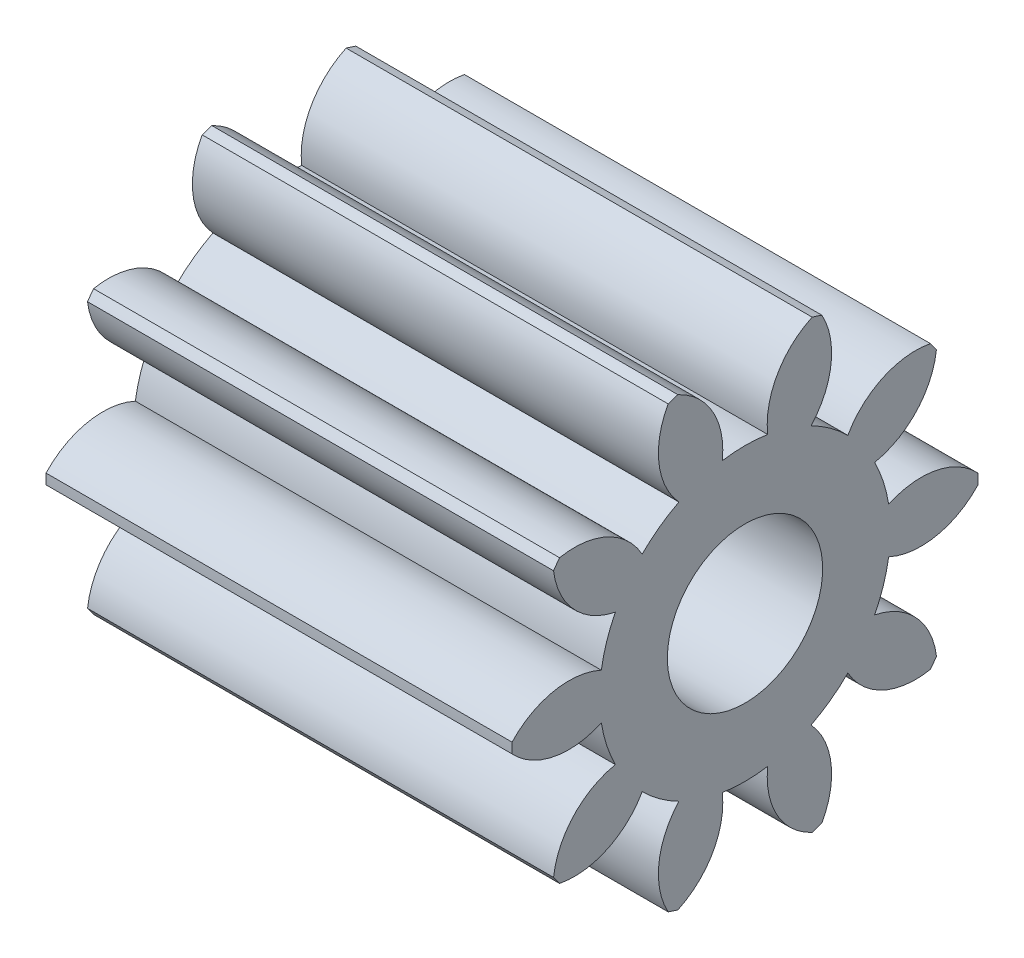
SolidWorks part; units mm, degrees
ref_plane "Plane1" through (0, 0, 0) normal (0, 0, 1) x (1, 0, 0)
ref_plane "Plane2" through (0, 0, 0) normal (0, 1, 0) x (1, 0, 0)
ref_plane "Plane3" through (0, 0, 0) normal (1, 0, 0) x (0, 0, -1)
sketch "HoldingSke" plane through (0, 0, 0) normal (0, 1, 0) x (1, 0, 0)
  line L0 (0, 0) -> (3.9392, -0.6946)
  line L1 (-15, 0) -> (100, 0) construction
  line L2 (0, 0) -> (-2.1039, 2.3779)
  line L3 (0, 0) -> (-11.863, 4.5341)
  line L4 (0, 0) -> (8.5048, 1.4996)
  line L5 (0, 0) -> (-46.8476, -17.4728)
  line L6 (0, 0) -> (-2.4869, -1.6779)
  line L7 (-2.1039, 2.3779) -> (8.6586, 51.2059)
  line L8 (-76.2, 54.61) -> (-76.1, 54.61)
  line L9 (-71.009, 38.7566) -> (-53.1078, 45.2721)
  line L10 (-76.2, 71.12) -> (104.1128, 71.12)
  line L11 (0, 0) -> (-3, 0)
  line L12 (-76.2, 101.6) -> (-76.192, 101.6)
  line L13 (24.9733, 27.94) -> (52.9518, 28.4284)
  line L14 (24.9733, 27.94) -> (24.9743, 27.94)
  line L15 (24.9733, 27.94) -> (100.4006, 29.5858)
  line L16 (-63.627, -0.25) -> (-12.827, -0.25)
  circle A0 centre (0, 0) radius 0.5
  circle A1 centre (0, 0) radius 0.9365
  circle A2 centre (0, 0) radius 37.5
  circle A3 centre (0, 0) radius 0.5
  dimension "MHD" = 1.873
  dimension "Hub_dia" = 75
  dimension "Bore" = 1
  dimension "MBD" = 1
  dimension "Num_teeth" = 10
  dimension "Pitch" = 4
  dimension "Overall_len" = 50
  dimension "Show_teeth" = 10
  dimension "Thickness" = 3
  dimension "OAL" = 50.0001
  dimension "T_dim" = 0.1
  dimension "Ap" = 20
  dimension "H" = 19.05
  dimension "Pitch_radius" = 180.3128
  dimension "Width" = 3
  dimension "Backlash" = 0.008
  dimension "Addendum_fac" = 1
  dimension "Dedendum_fac" = 1.25
  dimension "Clearance_fac" = 0.25
  dimension "Dedendum_add" = 0.001
  dimension "Module" = 0.25
sketch "BasProSke" plane through (0, 0, 0) normal (0, 1, 0) x (1, 0, 0)
  line L0 (-10, 0) -> (60, 0) construction
  line L1 (0, 0) -> (0, 1.5)
  line L2 (0, 0) -> (3, 0)
  line L3 (3, 0) -> (3, 1.5)
  line L4 (3, 1.5) -> (0, 1.5)
  dimension "Thickness" = 3
  dimension "Diameter" = 3
revolve "Base-Revolve" add sketch "BasProSke" angle 360 about L0
sketch "TooCutSke" plane through (0, 0, 0) normal (1, 0, 0) x (0, 0, -1)
  line L1 (0, 0) -> (0, 107) construction
  line L2 (0, 0) -> (-0.2095, 1.2323) construction
  line L3 (0, 0) -> (-0.7644, 2.3524) construction
  line L4 (-0.2095, 1.2323) -> (-0.3822, 1.1762) construction
  arc A0 (0.1463, 0.925) -> (-0.1463, 0.925) centre (0, 0) ccw
  arc A1 (0.4686, 1.4516) -> (-0.4686, 1.4516) centre (0, 0) ccw
  circle A2 centre (0, 0) radius 1.25 construction
  circle A3 centre (0, 0) radius 1.1746 construction
  arc A4 (-0.1463, 0.925) -> (-0.4686, 1.4516) centre (-0.6429, 0.983) ccw
  arc A5 (0.4686, 1.4516) -> (0.1463, 0.925) centre (0.6429, 0.983) ccw
  dimension "Root_dia" = 1.873
  dimension "Overcut_dia" = 3.0508
  dimension "Pitch_dia" = 2.5
  dimension "Base_dia" = 2.3492
  dimension "Flank_rad" = 0.5
  dimension "Half_ang" = 18
  dimension "Half_CT" = 0.1815
extrude "ToothCut" cut sketch "TooCutSke" along normal through all
fillet "Breaks" [suppressed] radius 0.005
fillet "RootFillets" [suppressed] radius 0.0635
pattern_circular "TeethCuts" count 10 every 36 about axis through (-10, 0, 0) along (1, 0, 0) of "ToothCut", "RootFillets", "Breaks"
sketch "HubNeaOneSke" plane through (0, 0, 0) normal (-1, 0, 0) x (0, 0, 1)
  circle A0 centre (0, 0) radius 0.9365
  dimension "Diameter" = 1.873
extrude "HubNearOne" [suppressed] add sketch "HubNeaOneSke" along normal blind 47.0001
sketch "HubNeaBotSke" plane through (0, 0, 0) normal (-1, 0, 0) x (0, 0, 1)
  circle A0 centre (0, 0) radius 0.9365
  dimension "Diameter" = 1.873
extrude "HubNearBoth" [suppressed] add sketch "HubNeaBotSke" along normal blind 23.5
ref_plane "FarPln" through (3, 0, 0) normal (1, 0, 0) x (0, 0, -1)
sketch "HubFarSke" plane through (3, 0, 0) normal (1, 0, 0) x (0, 0, -1)
  circle A0 centre (0, 0) radius 0.9365
  dimension "Diameter" = 1.873
extrude "HubFar" [suppressed] add sketch "HubFarSke" along normal blind 23.5
sketch "BorSke" plane through (0, 0, 0) normal (1, 0, 0) x (0, 0, -1)
  circle A0 centre (0, 0) radius 0.5
  dimension "Diameter" = 1
extrude "Bore" cut sketch "BorSke" along normal mid plane 100.0001
sketch "KeySke" plane through (0, 0, 0) normal (1, 0, 0) x (0, 0, -1)
  line L0 (-0.05, 0) -> (-0.05, 0.6)
  line L1 (-0.05, 0.6) -> (0.05, 0.6)
  line L2 (0.05, 0.6) -> (0.05, 0)
  line L3 (0, 0) -> (0, 34) construction
  line L4 (-0.05, 0) -> (0.05, 0)
  dimension "Offset" = 0.6
  dimension "Width" = 0.1
extrude "Keyway" [suppressed] cut sketch "KeySke" along normal mid plane 100.0001
pattern_circular "Keyway2" [suppressed] count 2 every 90 about axis through (-10, 0, 0) along (1, 0, 0)
equation "' \"Module@HoldingSke\" = 6.35"
equation "' \"Num_teeth@HoldingSke\" = 12"
equation "' \"Ap@HoldingSke\" =  20"
equation "' \"Ap@HoldingSke\" = 20"
equation "' \"Width@HoldingSke\" = 0.5 * 25.4"
equation "' \"Hub_dia@HoldingSke\"= 1 * 25.4"
equation "' \"Hub_dia@HoldingSke\" = 1 * 25.4"
equation "' \"Overall_len@HoldingSke\" = 1.0 * 25.4"
equation "' \"Bore@HoldingSke\" = 0.75 * 25.4"
equation "' \"T_dim@HoldingSke\" = 0.1 * 25.4"
equation "' \"Width@KeySke\" = 0.25 * 25.4"
equation "' \"Show_teeth@HoldingSke\" = 13"
equation "' \"Backlash@HoldingSke\" = 0.009 * 25.4"
equation "' \"Addendum_fac@HoldingSke\" = 1.0"
equation "' \"Dedendum_fac@HoldingSke\" = 1.25"
equation "' \"Dedendum_add@HoldingSke\" = 0.00005 * 25.4"
equation "' \"Clearance_fac@HoldingSke\" = 0.25"
equation "\"Pitch@HoldingSke\" = 1 / \"Module@HoldingSke\""
equation "\"Overcut_dia@TooCutSke\" = (\"Num_teeth@HoldingSke\" + 2 * \"Addendum_fac@HoldingSke\") / \"Pitch@HoldingSke\" + 0.002 * 25.4"
equation "\"Pitch_dia@TooCutSke\" = \"Num_teeth@HoldingSke\" / \"Pitch@HoldingSke\""
equation "\"Base_dia@TooCutSke\" = \"Num_teeth@HoldingSke\" / \"Pitch@HoldingSke\" * cos((\"Ap@HoldingSke\"  * 3.14159265 / 180))"
equation "\"Root_dia@TooCutSke\" = (\"Num_teeth@HoldingSke\" + 2) / \"Pitch@HoldingSke\" - 2 * (\"Addendum_fac@HoldingSke\" + \"Dedendum_fac@HoldingSke\") / \"Pitch@HoldingSke\" - \"Dedendum_add@HoldingSke\" * 2"
equation "\"Half_ang@TooCutSke\" = 180 / \"Num_teeth@HoldingSke\""
equation "\"Half_CT@TooCutSke\" = \"Num_teeth@HoldingSke\" / \"Pitch@HoldingSke\" * sin((3.14159265 / 2 / \"Num_teeth@HoldingSke\")) / 2 - 7 * \"Backlash@HoldingSke\" / 4"
equation "\"Flank_rad@TooCutSke\" = \"Num_teeth@HoldingSke\" / \"Pitch@HoldingSke\" / 5"
equation "\"Radius@RootFillets\" = \"Clearance_fac@HoldingSke\" / \"Pitch@HoldingSke\" + \"Dedendum_add@HoldingSke\""
equation "\"Break_rad@Breaks\" = 0.02 / \"Pitch@HoldingSke\""
equation "\"Thickness@HoldingSke\" = \"Width@HoldingSke\""
equation "\"OAL@HoldingSke\" = \"Thickness@HoldingSke\""
equation "\"MHD@HoldingSke\" = (\"Num_teeth@HoldingSke\" + 2) / \"Pitch@HoldingSke\" - 2 * (\"Addendum_fac@HoldingSke\" + \"Dedendum_fac@HoldingSke\")  / \"Pitch@HoldingSke\" - \"Dedendum_add@HoldingSke\" * 2"
equation "\"MBD@HoldingSke\" = (\"Num_teeth@HoldingSke\" + 2) / \"Pitch@HoldingSke\" - 2 * (\"Addendum_fac@HoldingSke\" + \"Dedendum_fac@HoldingSke\")  / \"Pitch@HoldingSke\" - \"Dedendum_add@HoldingSke\" * 2 - 0.002 * 25.4"
equation "\"MHD@HoldingSke\" = ((sgn( \"MHD@HoldingSke\" - \"Hub_dia@HoldingSke\" )-1)*( \"MHD@HoldingSke\" - \"Hub_dia@HoldingSke\" ))/-2+ \"Hub_dia@HoldingSke\""
equation "\"MBD@HoldingSke\" = ((sgn( \"MBD@HoldingSke\" - \"Bore@HoldingSke\" )-1)*( \"MBD@HoldingSke\" - \"Bore@HoldingSke\" ))/-2+ \"Bore@HoldingSke\""
equation "\"OAL@HoldingSke\" = ((sgn( \"OAL@HoldingSke\" - \"Overall_len@HoldingSke\" )+1)*( \"OAL@HoldingSke\" - \"Overall_len@HoldingSke\" ))/2 + \"Overall_len@HoldingSke\" + 0.000002 * 25.4"
equation "\"Num_teeth@TeethCuts\" = int( \"Show_teeth@HoldingSke\" ) + 1"
equation "\"Num_teeth@TeethCuts\" = ((sgn( \"Num_teeth@TeethCuts\" - \"Num_teeth@HoldingSke\" )-1)*( \"Num_teeth@TeethCuts\" - \"Num_teeth@HoldingSke\" ))/-2+ \"Num_teeth@HoldingSke\""
equation "\"Num_teeth@TeethCuts\" = ((sgn( \"Num_teeth@TeethCuts\" - 2.0)+1)*( \"Num_teeth@TeethCuts\" - 2.0))/2 +2.0"
equation "\"Angle@TeethCuts\" = 360.0 / \"Num_teeth@HoldingSke\""
equation "\"Diameter@BasProSke\" = (\"Num_teeth@HoldingSke\" + 2 * \"Addendum_fac@HoldingSke\") / \"Pitch@HoldingSke\""
equation "\"Thickness@BasProSke\"  = \"Thickness@HoldingSke\""
equation "' \"Fillet_rad@BasProSke\" =  \"Thickness@HoldingSke\" * 0.05"
equation "' \"Fillet_rad@BasProSke\" = \"Thickness@HoldingSke\" * 0.05"
equation "\"MHD@HoldingSke\" = ((sgn( \"MHD@HoldingSke\" - \"Root_dia@TooCutSke\" )-1)*( \"MHD@HoldingSke\" - \"Root_dia@TooCutSke\" ))/-2+ \"Root_dia@TooCutSke\""
equation "\"Diameter@HubNeaOneSke\" = \"MHD@HoldingSke\""
equation "\"Length@HubNearOne\" = \"OAL@HoldingSke\" - \"Thickness@BasProSke\""
equation "\"Diameter@HubNeaBotSke\" = \"MHD@HoldingSke\""
equation "\"Length@HubNearBoth\" = ( \"OAL@HoldingSke\" - \"Thickness@BasProSke\" ) / 2.0"
equation "\"Thickness@FarPln\" = \"Thickness@BasProSke\""
equation "\"Diameter@HubFarSke\" = \"MHD@HoldingSke\""
equation "\"Length@HubFar\" = ( \"OAL@HoldingSke\" - \"Thickness@BasProSke\" ) / 2.0"
equation "\"Diameter@BorSke\" = \"MBD@HoldingSke\""
equation "\"D1@Bore\" = \"OAL@HoldingSke\" * 2.0"
equation "\"D1@Keyway\" = \"OAL@HoldingSke\" * 2.0"
equation "\"Offset@KeySke\" = \"T_dim@HoldingSke\" + \"MBD@HoldingSke\" / 2.0"
